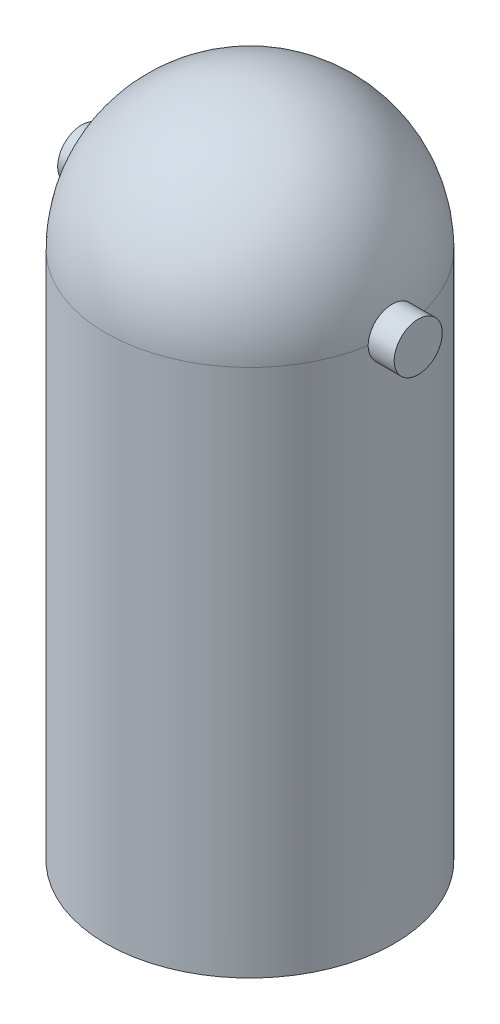
SolidWorks part; units mm, degrees
ref_plane "Front Plane" through (0, 0, 0) normal (0, 0, 1) x (1, 0, 0)
ref_plane "Top Plane" through (0, 0, 0) normal (0, 1, 0) x (1, 0, 0)
ref_plane "Right Plane" through (0, 0, 0) normal (1, 0, 0) x (0, 0, -1)
sketch "Sketch1" plane through (0, 0, 0) normal (0, 1, 0) x (1, 0, 0)
  circle A0 centre (0, 0) radius 30
  dimension "D1" = 60
extrude "Boss-Extrude1" add sketch "Sketch1" along normal blind 110
sketch "Sketch5" plane through (0, 0, 0) normal (0, 0, 1) x (1, 0, 0)
  line L0 (-30, 110) -> (0, 110)
  line L1 (0, 110) -> (30, 110)
  arc A0 (-30, 110) -> (30, 110) centre (0, 110) cw
  dimension "D1" = 30
revolve "Revolve1" add sketch "Sketch5" angle 360 about L0
sketch "Sketch6" plane through (0, 0, 0) normal (0, -1, 0) x (1, 0, 0)
  circle A0 centre (0, 0) radius 20
  dimension "D1" = 40
extrude "Cut-Extrude2" cut sketch "Sketch6" against normal blind 100
sketch "Sketch7" plane through (0, 0, 0) normal (1, 0, 0) x (0, 0, -1)
  line L0 (-30, 110) -> (30, 110) construction
  circle A0 centre (0, 110) radius 5
  dimension "D1" = 10
extrude "Boss-Extrude2" add sketch "Sketch7" along normal blind 35
mirror "Mirror1" about plane through (0, 0, 0) normal (1, 0, 0) of "Boss-Extrude2"
